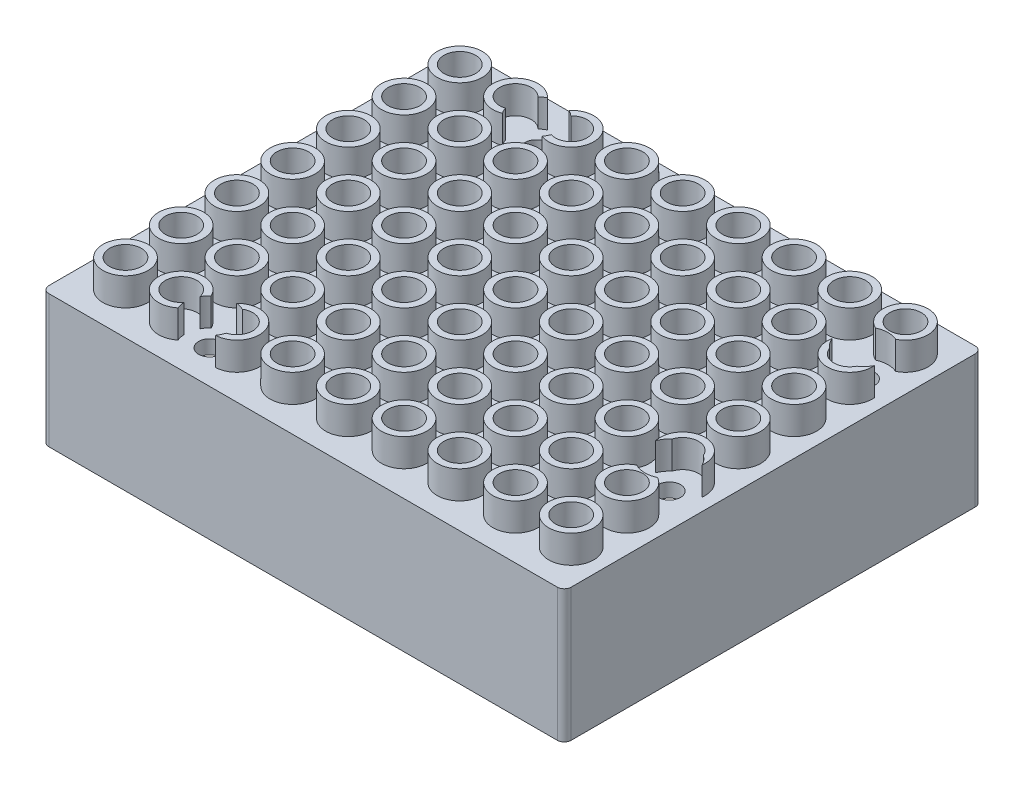
SolidWorks part; units mm, degrees
ref_plane "Front Plane" through (0, 0, 0) normal (0, 0, 1) x (1, 0, 0)
ref_plane "Top Plane" through (0, 0, 0) normal (0, 1, 0) x (1, 0, 0)
ref_plane "Right Plane" through (0, 0, 0) normal (1, 0, 0) x (0, 0, -1)
sketch "Sketch1" plane through (0, 0, 0) normal (0, 1, 0) x (1, 0, 0)
  line L1 (-37.5, -30) -> (37.5, -30)
  line L2 (-37.5, -30) -> (-37.5, 30)
  line L3 (-37.5, 30) -> (37.5, 30)
  line L4 (37.5, -30) -> (37.5, 30)
  line L5 (-37.5, -30) -> (37.5, 30) construction
  line L6 (-37.5, 30) -> (37.5, -30) construction
  point P0 (0, 0)
  dimension "D1" = 75
  dimension "D2" = 60
extrude "Boss-Extrude1" add sketch "Sketch1" along normal blind 19.05
fillet "Fillet1" radius 1 4 edges at (-37.5, 9.525, 30) (-37.5, 9.525, -30) (37.5, 9.525, -30) (37.5, 9.525, 30)
sketch "Sketch3" plane through (0, 19.05, 0) normal (0, 1, 0) x (1, 0, 0)
  line L0 (-37.5, -18.85) -> (-34, -18.85)
  line L1 (-37.5, 29) -> (-37.5, -29) construction
  line L2 (-34, -18.85) -> (-34, -28.25)
  line L3 (-34, -28.25) -> (33.125, -28.25)
  line L4 (33.125, -28.25) -> (33.125, -15.25)
  line L5 (33.125, -15.25) -> (36, -12.375)
  line L6 (36, -12.375) -> (36, 20.375)
  line L7 (36, 20.375) -> (33.125, 23.25)
  line L8 (33.125, 23.25) -> (33.125, 26.75)
  line L9 (33.125, 26.75) -> (-34, 26.75)
  line L10 (-34, 26.75) -> (-34, -6)
  line L11 (-34, -6) -> (-37.5, -6)
  line L12 (-37.5, -6) -> (-37.5, -18.85)
  line L13 (-36.5, -30) -> (36.5, -30) construction
  dimension "D1" = 55
  dimension "D2" = 70
  dimension "D3" = 32.75
  dimension "D4" = 3.5
  dimension "D5" = 13
  dimension "D6" = 225
  dimension "D7" = 32.75
  dimension "D8" = 9.4
  dimension "D9" = 1.75
  dimension "D10" = 3.5
extrude "Arduino Cavity" cut sketch "Sketch3" against normal blind 19.125 from offset 2 offset against normal yes
sketch "Sketch4" plane through (-37.5, 0, 0) normal (-1, 0, 0) x (0, 0, 1)
  circle A0 centre (-17.925, 6.4) radius 5.5
  arc A1 (-21.925, 6.4) -> (-13.925, 6.4) centre (-17.925, 6.4) ccw construction
  dimension "D1" = 11
extrude "9V Barrel Plug hole" cut sketch "Sketch4" against normal blind 19.125
sketch "Sketch5" plane through (0, 19.05, 0) normal (0, 1, 0) x (1, 0, 0)
  line L0 (-37.5, 29) -> (-37.5, -29) construction
  line L1 (-36.5, -30) -> (36.5, -30) construction
  circle A0 centre (-31.5, -24) radius 3.2375
  dimension "D1" = 6.475
  dimension "D2" = 6
  dimension "D3" = 6
extrude "Bump 1" add sketch "Sketch5" along normal blind 4
sketch "Sketch6" plane through (0, 23.05, 0) normal (0, 1, 0) x (1, 0, 0)
  circle A0 centre (-31.5, -24) radius 2.275
  circle A1 centre (-31.5, -24) radius 3.2375 construction
  dimension "D1" = 4.55
extrude "Cut-Extrude3" cut sketch "Sketch6" against normal up to surface (4 mm away) up to face at (-31.5, 19.05, 20.7625)
pattern_linear "LPattern1" count 7 spacing 8 along (0, 0, -1) of "Bump 1", "Cut-Extrude3"
pattern_linear "LPattern2" count 9 spacing 8 along (1, 0, 0) of "LPattern1", "Bump 1", "Cut-Extrude3"
sketch "Sketch2" plane through (0, 0, 0) normal (0, -1, 0) x (-1, 0, 0)
  line L0 (-36.5, 30) -> (36.5, 30) construction
  line L2 (37.5, 30) -> (37.5, -30) construction
  circle A0 centre (18.2, -25.2) radius 1.6
  circle A1 centre (19.5, 23) radius 1.6
  circle A2 centre (-32.6, -10) radius 1.6
  circle A3 centre (-32.6, 17.9) radius 1.6
  dimension "D1" = 3.2
  dimension "D2" = 3.2
  dimension "D3" = 3.2
  dimension "D4" = 3.2
  dimension "D5" = 50.8
  dimension "D6" = 15.2
  dimension "D7" = 1.3
  dimension "D8" = 27.9
  dimension "D9" = 5.1
  dimension "D10" = 7
  dimension "D11" = 18
extrude "Mount Holes" cut sketch "Sketch2" against normal through all both and the other way through all
sketch "Sketch7" plane through (0, 19.05, 0) normal (0, 1, 0) x (1, 0, 0)
  circle A0 centre (32.6, -10) radius 3.5
  circle A1 centre (32.6, 17.9) radius 3.5
  circle A2 centre (-18.2, -25.2) radius 3.5
  circle A3 centre (-19.5, 23) radius 3.5
  arc A4 (31.383, -11.0387) -> (33.9145, -10.9121) centre (32.6, -10) ccw construction
  dimension "D1" = 7
  dimension "D2" = 7
  dimension "D3" = 7
  dimension "D4" = 7
extrude "Cut-Extrude4" cut sketch "Sketch7" along normal up to surface (4 mm away) up to face at (32.5, 23.05, 26.275)
equation "\"D2@Sketch2\"=\"D1@Sketch2\""
equation "\"D3@Sketch2\"=\"D1@Sketch2\""
equation "\"D4@Sketch2\"=\"D1@Sketch2\""
equation "\"D2@Sketch7\"=\"D1@Sketch7\""
equation "\"D3@Sketch7\"=\"D1@Sketch7\""
equation "\"D4@Sketch7\"=\"D1@Sketch7\""
